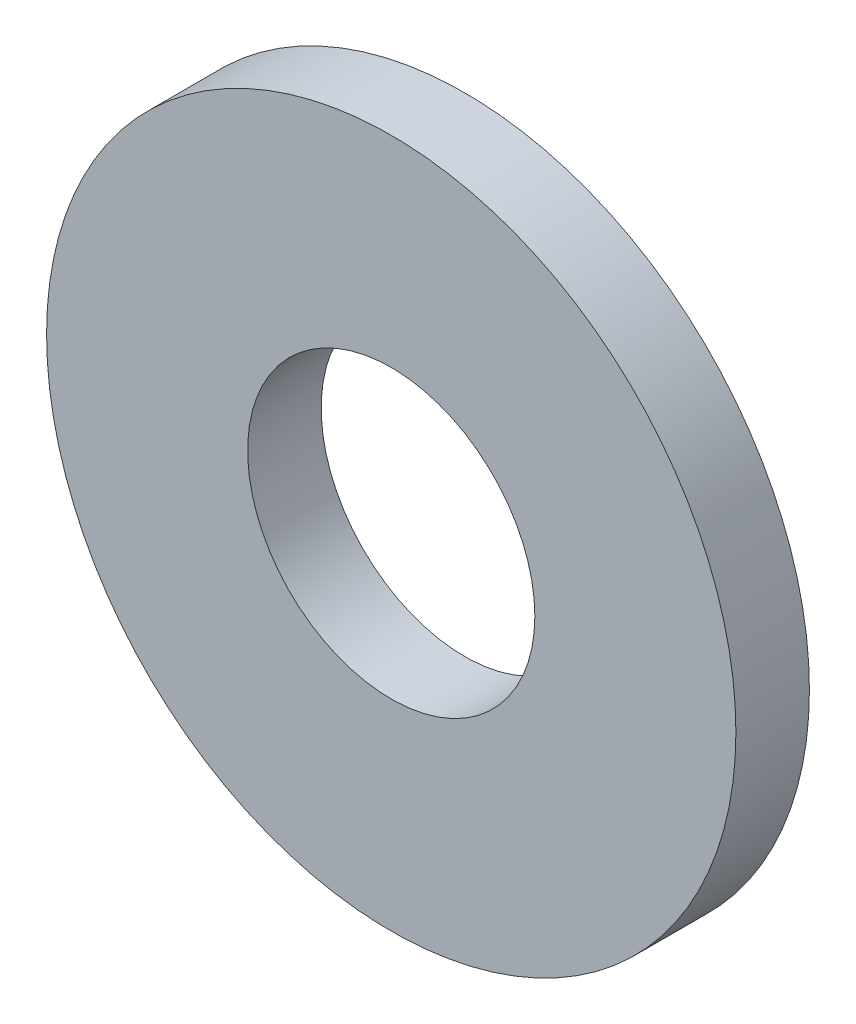
SolidWorks part; units mm, degrees
ref_plane "Front Plane" through (0, 0, 0) normal (0, 0, 1) x (1, 0, 0)
ref_plane "Top Plane" through (0, 0, 0) normal (0, 1, 0) x (1, 0, 0)
ref_plane "Right Plane" through (0, 0, 0) normal (1, 0, 0) x (0, 0, -1)
sketch "Sketch1" plane through (0, 0, 0) normal (0, 0, 1) x (1, 0, 0)
  circle A0 centre (0, 0) radius 3.9688
  circle A1 centre (0, 0) radius 9.525
  dimension "ID" = 7.9375
  dimension "OD" = 19.05
extrude "Extrude1" add sketch "Sketch1" against normal blind 2.032
